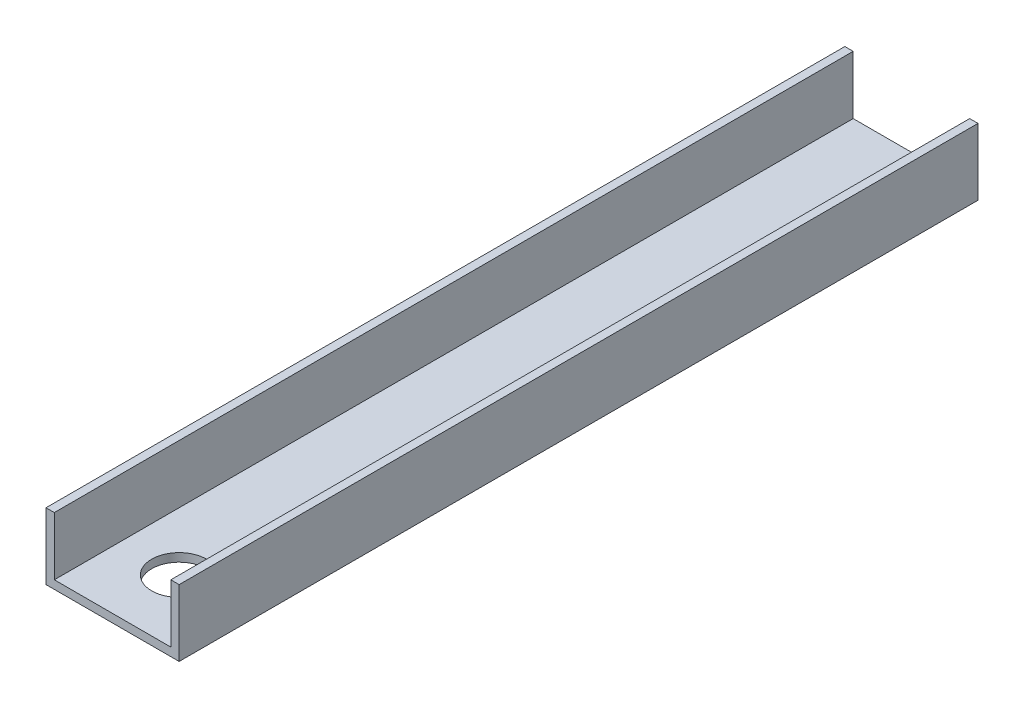
SolidWorks part; units mm, degrees
ref_plane "Front Plane" through (0, 0, 0) normal (0, 0, 1) x (1, 0, 0)
ref_plane "Top Plane" through (0, 0, 0) normal (0, 1, 0) x (1, 0, 0)
ref_plane "Right Plane" through (0, 0, 0) normal (1, 0, 0) x (0, 0, -1)
sketch "Sketch1" plane through (0, 0, 0) normal (0, 0, 1) x (1, 0, 0)
  line L1 (0, 0) -> (50.8, 0)
  line L2 (0, 0) -> (0, 25.4)
  line L3 (0, 25.4) -> (50.8, 25.4)
  line L4 (50.8, 0) -> (50.8, 25.4)
extrude "Boss-Extrude1" add sketch "Sketch1" along normal blind 304.8
sketch "Sketch2" plane through (0, 0, 0) normal (0, 0, -1) x (-1, 0, 0)
  line L0 (-50.8, 25.4) -> (0, 25.4) construction
  line L1 (-47.625, 25.4) -> (-3.175, 25.4)
  line L2 (-47.625, 25.4) -> (-47.625, 3.175)
  line L3 (-47.625, 3.175) -> (-3.175, 3.175)
  line L4 (-3.175, 25.4) -> (-3.175, 3.175)
  line L5 (0, 25.4) -> (0, 0) construction
  line L6 (-50.8, 0) -> (-50.8, 25.4) construction
  line L7 (0, 0) -> (-50.8, 0) construction
  dimension "D1" = 3.175
  dimension "D2" = 3.175
  dimension "D3" = 3.175
extrude "Cut-Extrude1" cut sketch "Sketch2" against normal through all
sketch "Sketch3" plane through (0, 3.175, 0) normal (0, 1, 0) x (1, 0, 0)
  line L0 (25.4, -304.8) -> (25.4, -279.4) construction
  line L1 (47.625, -304.8) -> (3.175, -304.8) construction
  circle A0 centre (25.4, -279.4) radius 10.4775
extrude "Cut-Extrude2" cut sketch "Sketch3" against normal through all
